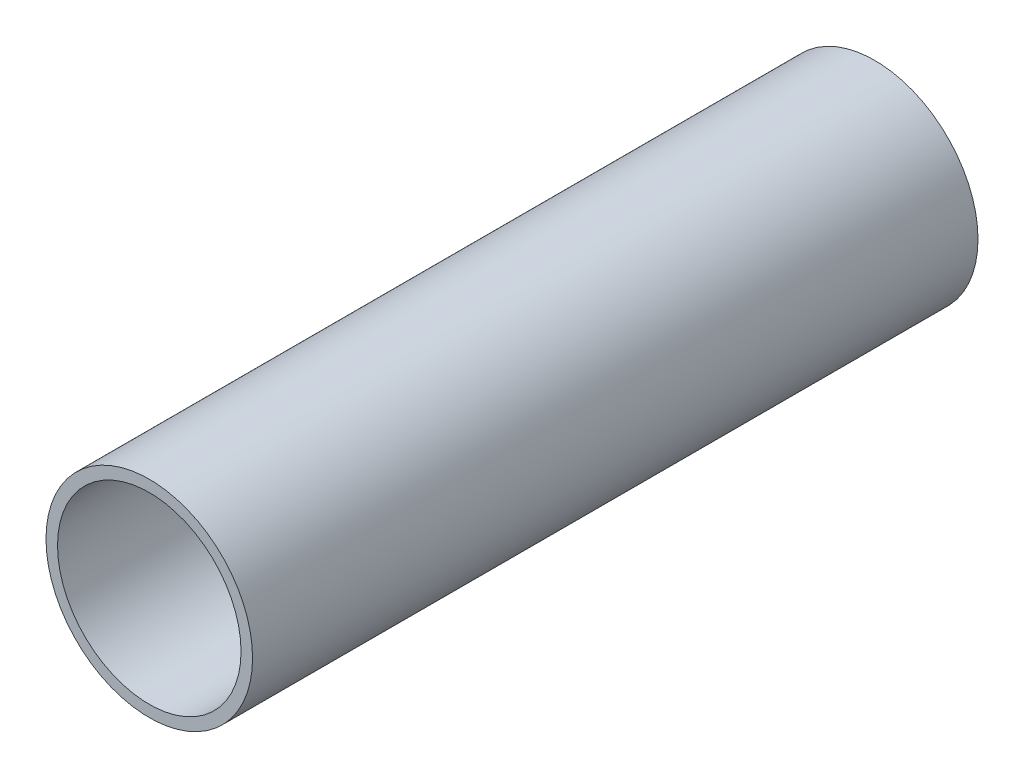
SolidWorks part; units mm, degrees
ref_plane "Front Plane" through (0, 0, 0) normal (0, 0, 1) x (1, 0, 0)
ref_plane "Top Plane" through (0, 0, 0) normal (0, 1, 0) x (1, 0, 0)
ref_plane "Right Plane" through (0, 0, 0) normal (1, 0, 0) x (0, 0, -1)
sketch "Sketch1" plane through (0, 0, 0) normal (0, 0, 1) x (1, 0, 0)
  circle A0 centre (0, 0) radius 50.595
  circle A1 centre (0, 0) radius 56.945
  dimension "D1" = 101.19
  dimension "D2" = 6.35
extrude "Boss-Extrude1" add sketch "Sketch1" along normal blind 400
